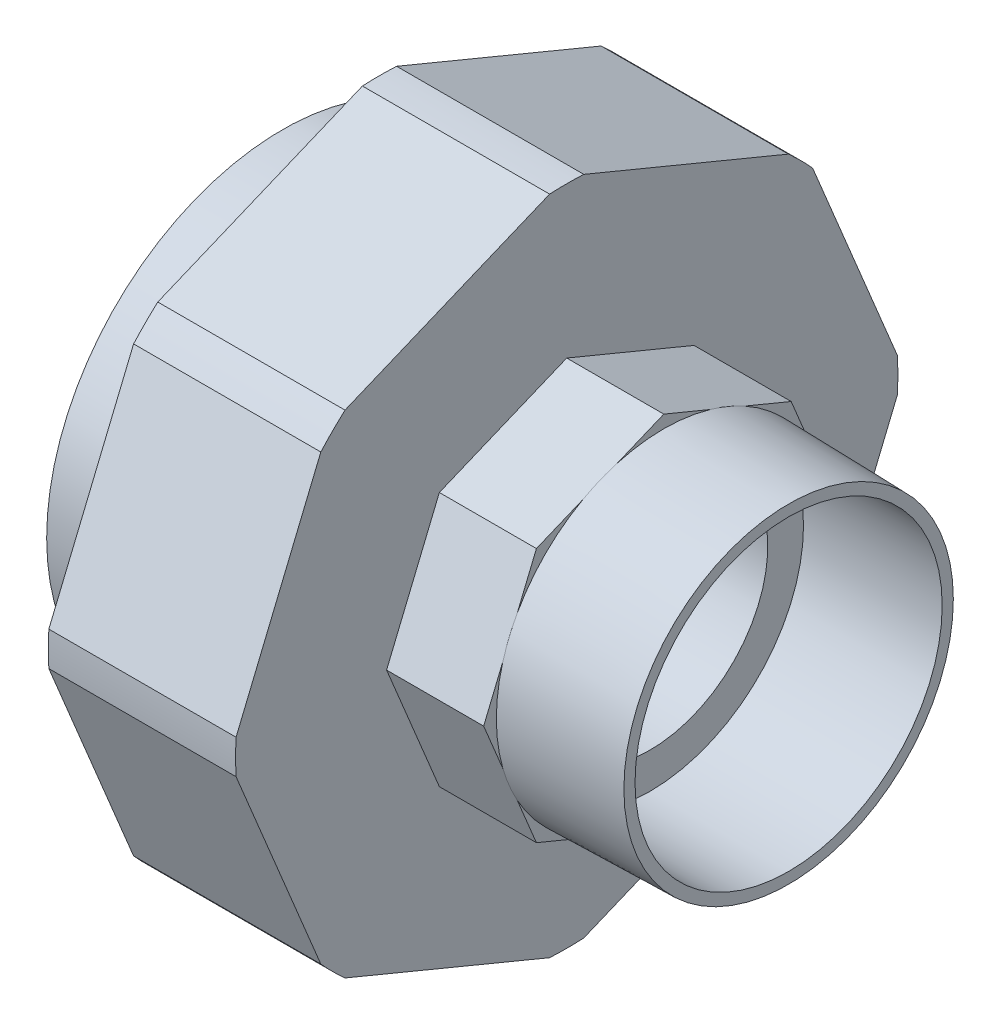
SolidWorks part; units mm, degrees
ref_plane "Front Plane" through (0, 0, 0) normal (0, 0, 1) x (1, 0, 0)
ref_plane "Top Plane" through (0, 0, 0) normal (0, 1, 0) x (1, 0, 0)
ref_plane "Right Plane" through (0, 0, 0) normal (1, 0, 0) x (0, 0, -1)
sketch "Sketch1" plane through (0, 0, 0) normal (0, 0, 1) x (1, 0, 0)
  line L0 (-32.3141, -25) -> (-8.8141, -25)
  line L1 (-8.8141, -25) -> (-8.8141, -17)
  line L2 (-8.8141, -17) -> (20.6859, -17)
  line L3 (20.6859, -17) -> (20.6859, -22.15)
  line L4 (20.6859, -22.15) -> (40.6859, -22.15)
  line L5 (40.6859, -22.15) -> (40.6859, -23.7572)
  line L7 (8.6859, -34.7405) -> (8.6859, -47.75)
  line L8 (8.6859, -47.75) -> (-18.3141, -47.75)
  line L9 (-18.3141, -47.75) -> (-18.3141, -34)
  line L10 (-18.3141, -34) -> (-32.3141, -34)
  line L11 (-32.3141, -34) -> (-32.3141, -25)
  line L12 (0, 0) -> (30.2034, 0) construction
  line L13 (8.6859, -34.7405) -> (22.6859, -34.7405)
  line L14 (22.6859, -34.7405) -> (22.6859, -24.15)
  line L15 (22.6859, -24.15) -> (40.6859, -23.7572)
  point P23 (-18.3141, -47.75)
  dimension "D10" = 18
  dimension "D1" = 25
  dimension "D2" = 9
  dimension "D3" = 23.5
  dimension "D4" = 14
  dimension "D5" = 73
  dimension "D6" = 47.75
  dimension "D7" = 8
  dimension "D8" = 24.15
  dimension "D9" = 22.15
  dimension "D11" = 1.25
  dimension "D12" = 27
  dimension "D13" = 14
  dimension "D14" = 20
revolve "Revolve1" add sketch "Sketch1" angle 360 about L12
sketch "Sketch2" plane through (8.6859, 0, 0) normal (1, 0, 0) x (0, 0, -1)
  line L1 (0, 48.7076) -> (-34.4415, 34.4415)
  line L2 (-34.4415, 34.4415) -> (-48.7076, 0)
  line L3 (-48.7076, 0) -> (-34.4415, -34.4415)
  line L4 (-34.4415, -34.4415) -> (0, -48.7076)
  line L5 (0, -48.7076) -> (34.4415, -34.4415)
  line L6 (34.4415, -34.4415) -> (48.7076, 0)
  line L7 (48.7076, 0) -> (34.4415, 34.4415)
  line L8 (34.4415, 34.4415) -> (0, 48.7076)
  circle A0 centre (0, 0) radius 45 construction
  circle A1 centre (0, 0) radius 61.4155
  dimension "D1" = 90
extrude "Cut-Extrude1" cut sketch "Sketch2" against normal up to next
sketch "Sketch3" plane through (22.6859, 0, 0) normal (1, 0, 0) x (0, 0, -1)
  line L1 (0, 25.9774) -> (-18.3688, 18.3688)
  line L2 (-18.3688, 18.3688) -> (-25.9774, 0)
  line L3 (-25.9774, 0) -> (-18.3688, -18.3688)
  line L4 (-18.3688, -18.3688) -> (0, -25.9774)
  line L5 (0, -25.9774) -> (18.3688, -18.3688)
  line L6 (18.3688, -18.3688) -> (25.9774, 0)
  line L7 (25.9774, 0) -> (18.3688, 18.3688)
  line L8 (18.3688, 18.3688) -> (0, 25.9774)
  circle A0 centre (0, 0) radius 24 construction
  circle A1 centre (0, 0) radius 40.1221
  dimension "D1" = 48
extrude "Cut-Extrude2" cut sketch "Sketch3" against normal up to surface (14 mm away) up to face at (8.6859, 0, 34.7405)
